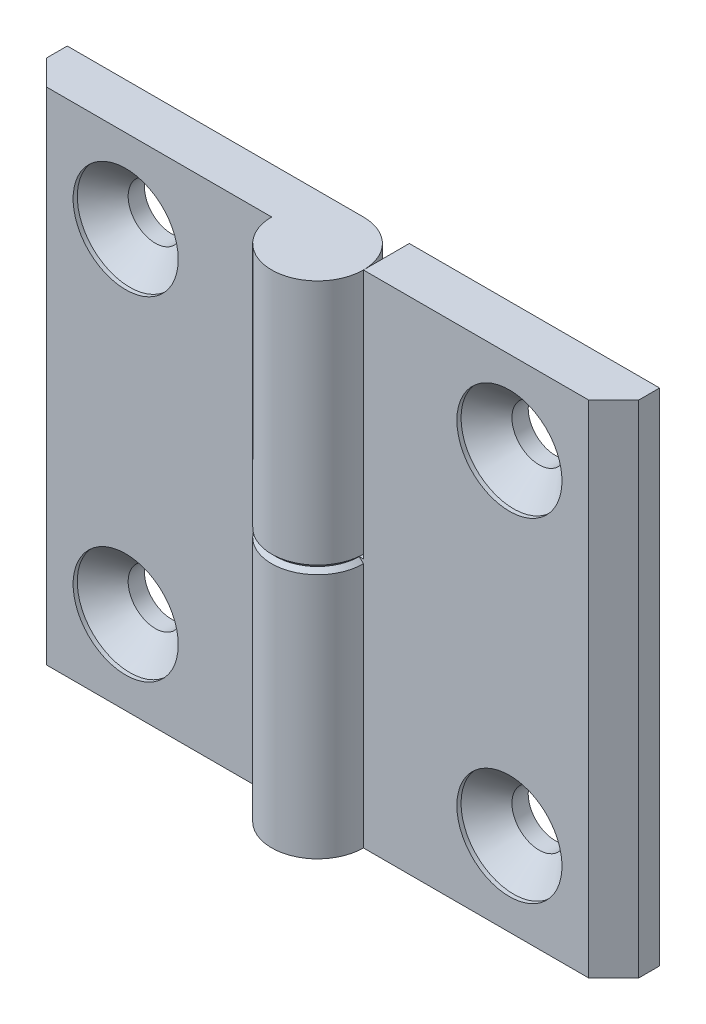
SolidWorks part; units mm, degrees
material "Алюминиевый сплав"
ref_plane "Спереди" through (0, 0, 0) normal (0, 0, 1) x (1, 0, 0)
ref_plane "Сверху" through (0, 0, 0) normal (0, 1, 0) x (1, 0, 0)
ref_plane "Справа" through (0, 0, 0) normal (1, 0, 0) x (0, 0, -1)
sketch "Эскиз1" plane through (0, 0, 0) normal (0, 1, 0) x (1, 0, 0)
  line L0 (0, 5.5) -> (-35.5, 5.5)
  line L1 (-35.5, 5.5) -> (-35.5, 3)
  line L2 (-35.5, 3) -> (-32.5, 0)
  line L3 (-32.5, 0) -> (-5.5, 0)
  line L4 (0, 0) -> (0, 10.5526) construction
  arc A0 (-5.5, 0) -> (0, 5.5) centre (0, 0) ccw
  dimension "D1" = 71
  dimension "D2" = 5.5
  dimension "D3" = 2.5
  dimension "D4" = 45
extrude "Бобышка-Вытянуть1" add sketch "Эскиз1" along normal mid plane 60
sketch "Эскиз3" plane through (0, 0, 0) normal (0, 0, 1) x (1, 0, 0)
  line L5 (-5.5, 30) -> (-5.5, -30) construction
  line L6 (5.5, -30) -> (-5.5, -30)
  line L7 (5.5, -30) -> (5.5, 0)
  line L8 (5.5, 0) -> (-5.5, 0)
  line L9 (-5.5, -30) -> (-5.5, 0)
extrude "Вырез-Вытянуть1" cut sketch "Эскиз3" against normal through all and the other way through all
hole_wizard "Зенковка для винта с полупотайной головкой M61" positions "Эскиз4" profile "Эскиз6" countersink size "M6" standard "ISO" end condition through all
sketch "Эскиз4" plane through (0, 0, 0) normal (0, 0, 1) x (1, 0, 0)
  line L0 (-23, 20) -> (-23, -20)
  line L2 (0, 0) -> (0, 18.9001) construction
  point P0 (-23, 20)
  point P2 (-23, -20)
  point P9 (-23, 0)
  dimension "D1" = 40
  dimension "D2" = 46
sketch "Эскиз6" plane through (-23, 20, 0) normal (1, 0, 0) x (0, -1, 0)
  line L0 (0, 0) -> (0, 5.5)
  line L1 (0, 5.5) -> (3.25, 5.5)
  line L2 (3.25, 5.5) -> (3.25, 3.55)
  line L3 (3.25, 3.55) -> (6.3, 0.5)
  line L4 (6.3, 0.5) -> (6.3, 0)
  line L6 (6.3, 0) -> (0, 0)
  line L7 (-3.25, 3.55) -> (-6.3, 0.5) construction
  line L11 (0, -6.35) -> (0, 107.95) construction
  dimension "Диаметр сквозного отверстия" = 6.5
  dimension "Глубина сквозного отверстия" = 5.5
  dimension "Диаметр зенковки" = 12.6
  dimension "Угол зенковки" = 90
  dimension "Утопленность" = 0.5
chamfer "Фаска1" distance 0.5 angle 45 2 edges at (-2.75, 0, -5.5) (3.8891, 0, 3.8891)
sketch "Угол раскрытия" plane through (0, 0, 0) normal (0, 1, 0) x (1, 0, 0)
  line L0 (0, 0) -> (0, -10)
  line L7 (0, 5.5) -> (-35.5, 5.5) construction
  dimension "D1" = 10
  dimension "D2" = 90
pattern_circular "Круговой массив1" count 2 over 360 about axis through (0, 0, 0) along (0, 0, 1) of bodies 106
